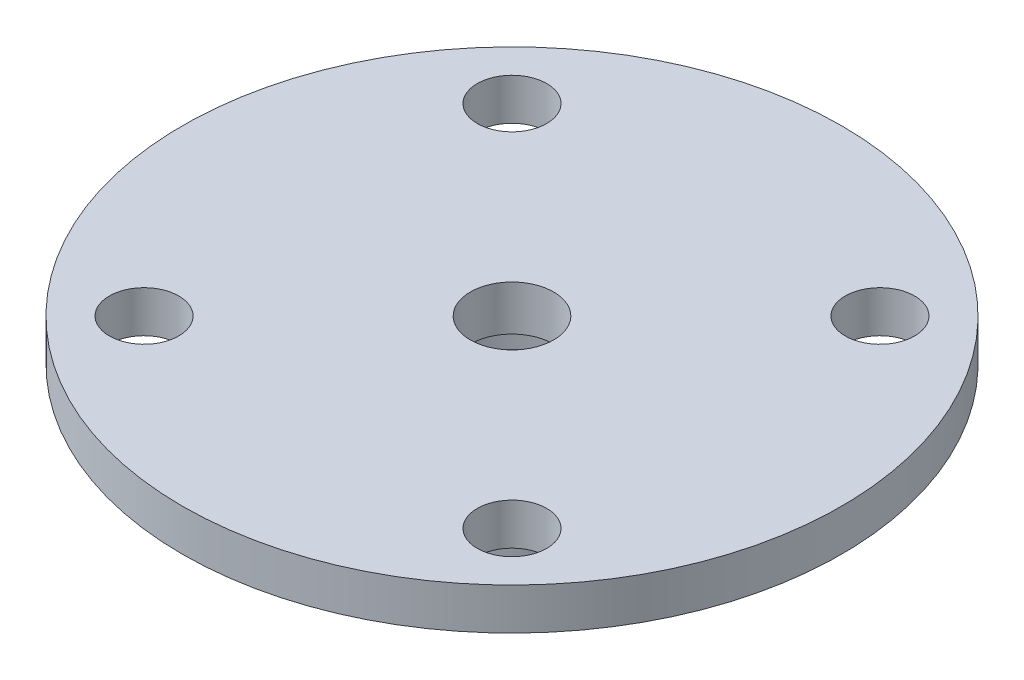
SolidWorks part; units mm, degrees
material "PF"
ref_plane "Alzado" through (0, 0, 0) normal (0, 0, 1) x (1, 0, 0)
ref_plane "Planta" through (0, 0, 0) normal (0, 1, 0) x (1, 0, 0)
ref_plane "Vista lateral" through (0, 0, 0) normal (1, 0, 0) x (0, 0, -1)
sketch "Croquis1" plane through (0, 0, 0) normal (0, 1, 0) x (1, 0, 0)
  line L6 (-25.2405, -3.0828) -> (-19.9372, -8.3861) construction
  line L7 (-19.9372, -8.3861) -> (-14.6339, -13.6894) construction
  line L8 (-25.2405, -13.6894) -> (-14.6339, -3.0828) construction
  circle A0 centre (-14.6339, -3.0828) radius 1
  circle A1 centre (-14.6339, -13.6894) radius 1
  circle A2 centre (-25.2405, -13.6894) radius 1
  circle A3 centre (-25.2405, -3.0828) radius 1
  circle A4 centre (-19.9372, -8.3861) radius 9.5
extrude "Saliente-Extruir1" add sketch "Croquis1" along normal blind 1.2
sketch "Croquis2" plane through (0, 0, 0) normal (0, -1, 0) x (-1, 0, 0)
  line L0 (19.9372, 1.1139) -> (19.9372, -17.8861) construction
  circle A0 centre (19.9372, -8.3861) radius 9.5 construction
  circle A1 centre (19.9372, -8.3861) radius 4.5
extrude "Saliente-Extruir2" add sketch "Croquis2" along normal blind 2
sketch "Croquis3" plane through (0, -2, 0) normal (0, -1, 0) x (-1, 0, 0)
  line L0 (19.9372, -3.8861) -> (19.9372, -12.8861) construction
  circle A0 centre (19.9372, -8.3861) radius 4.5 construction
  circle A1 centre (19.9372, -8.3861) radius 3.35
sketch "Sketch1" plane through (0, 1.2, 0) normal (0, 1, 0) x (1, 0, 0)
  circle A1 centre (-19.9372, -8.3861) radius 1.2
extrude "Cut-Extrude2" cut sketch "Sketch1" against normal blind 5
extrude "Cut-Extrude3" cut sketch "Croquis3" against normal blind 1.9 contours A1
